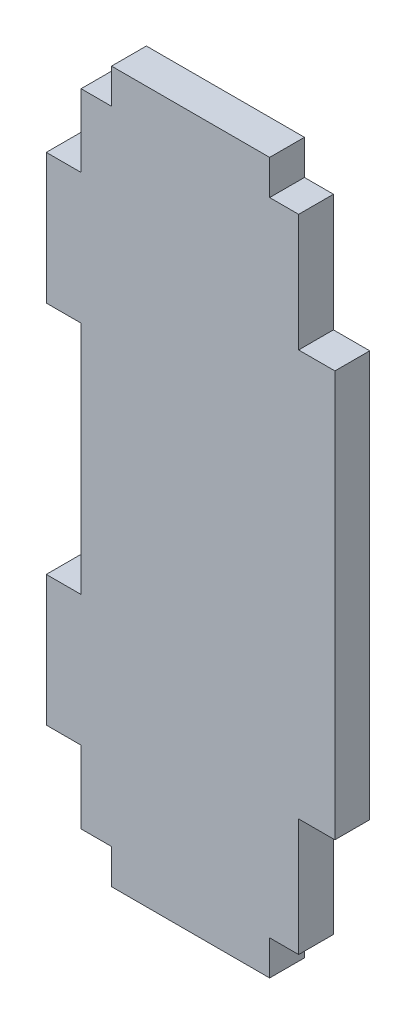
SolidWorks part; units mm, degrees
ref_plane "Front Plane" through (0, 0, 0) normal (0, 0, 1) x (1, 0, 0)
ref_plane "Top Plane" through (0, 0, 0) normal (0, 1, 0) x (1, 0, 0)
ref_plane "Right Plane" through (0, 0, 0) normal (1, 0, 0) x (0, 0, -1)
sketch "Sketch1" plane through (0, 0, 0) normal (0, 0, 1) x (1, 0, 0)
  line L0 (-3.175, -13.335) -> (0, -13.335)
  line L1 (0, -13.335) -> (0, -48.895)
  line L2 (-3.175, -48.895) -> (-3.175, -59.182)
  line L3 (-3.175, -62.23) -> (-3.175, 0) construction
  line L11 (-5.715, -3.048) -> (-5.715, 0)
  line L12 (-19.558, -3.048) -> (-19.558, 0)
  line L13 (-5.715, 0) -> (-19.558, 0)
  line L14 (-19.558, -59.182) -> (-19.558, -62.23)
  line L15 (-19.558, -62.23) -> (-5.715, -62.23)
  line L16 (-5.715, -59.182) -> (-5.715, -62.23)
  line L17 (-5.715, -59.182) -> (-3.175, -59.182)
  line L18 (-3.175, -3.048) -> (-5.715, -3.048)
  line L21 (-3.175, -48.895) -> (0, -48.895)
  line L22 (-3.175, -3.048) -> (-3.175, -13.335)
  line L23 (-3.175, -48.895) -> (-3.175, -59.182)
  line L24 (-19.558, -59.182) -> (-22.225, -59.182)
  line L25 (-22.225, -59.182) -> (-22.225, -52.832)
  line L26 (-22.225, -52.832) -> (-25.273, -52.832)
  line L27 (-25.273, -52.832) -> (-25.273, -41.402)
  line L28 (-25.273, -41.402) -> (-22.225, -41.402)
  line L29 (-22.225, -41.402) -> (-22.225, -20.828)
  line L30 (-22.225, -20.828) -> (-25.273, -20.828)
  line L31 (-25.273, -20.828) -> (-25.273, -9.398)
  line L32 (-25.273, -9.398) -> (-22.225, -9.398)
  line L33 (-22.225, -9.398) -> (-22.225, -3.048)
  line L34 (-22.225, -3.048) -> (-19.558, -3.048)
  dimension "D1" = 17.78
  dimension "D2" = 17.78
  dimension "D3" = 11.43
  dimension "D4" = 11.43
  dimension "D5" = 3.048
extrude "Boss-Extrude1" add sketch "Sketch1" along normal blind 3.048 contours L34 L33 L32 L31 L30 L29 L28 L27 L26 L25 L24 L14 L15 L16 L17 L2 L21 L1 L0 L22 L18 L11 L13 L12
